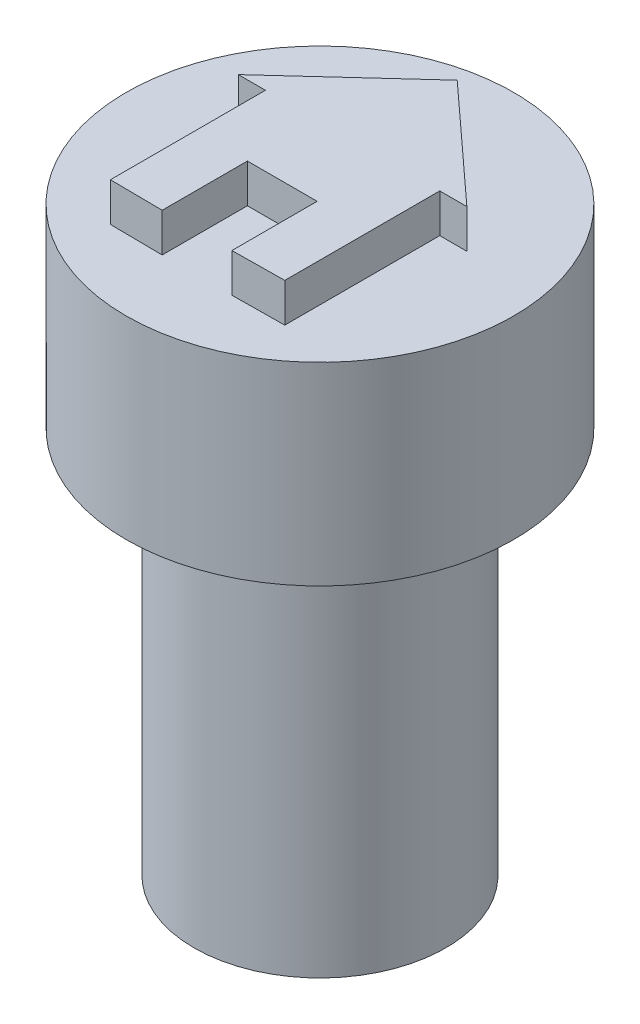
SolidWorks part; units mm, degrees
ref_plane "Front Plane" through (0, 0, 0) normal (0, 0, 1) x (1, 0, 0)
ref_plane "Top Plane" through (0, 0, 0) normal (0, 1, 0) x (1, 0, 0)
ref_plane "Right Plane" through (0, 0, 0) normal (1, 0, 0) x (0, 0, -1)
sketch "Sketch1" plane through (0, 0, 0) normal (0, 1, 0) x (1, 0, 0)
  circle A0 centre (0, 0) radius 3.25
  dimension "D1" = 6.5
extrude "Boss-Extrude1" add sketch "Sketch1" along normal blind 10 contours A0
sketch "Sketch2" plane through (0, 0, 0) normal (0, -1, 0) x (1, 0, 0)
  circle A1 centre (0, 0) radius 1.75
  dimension "D1" = 3.5
extrude "Cut-Extrude1" cut sketch "Sketch2" against normal blind 2.5
sketch "Sketch6" plane through (0, 10, 0) normal (0, 1, 0) x (1, 0, 0)
  circle A0 centre (0, 0) radius 5
  dimension "D1" = 10
extrude "Boss-Extrude2" add sketch "Sketch6" along normal blind 5 contours A0
sketch "Sketch7" plane through (0, 15, 0) normal (0, 1, 0) x (1, 0, 0)
  line L0 (-2.25, 0) -> (2.25, 0) construction
  line L1 (-2.25, 2.25) -> (2.25, 2.25)
  line L2 (-2.25, 2.25) -> (-2.25, -2.25)
  line L3 (-2.25, -2.25) -> (2.25, -2.25)
  line L4 (2.25, 2.25) -> (2.25, -2.25)
  line L5 (-2.25, 2.25) -> (2.25, -2.25) construction
  line L6 (-2.25, -2.25) -> (2.25, 2.25) construction
  line L7 (-2.25, 2.25) -> (-2.25, -2.25)
  point P0 (0, -0.8558)
  dimension "D1" = 4.5
  dimension "D2" = 4.5
sketch "Sketch9" plane through (0, 15, 0) normal (0, 1, 0) x (1, 0, 0)
  line L0 (0, 0.8425) -> (0, 3.5425) construction
  line L1 (-2.25, 0.8425) -> (2.25, 0.8425)
  line L2 (-2.25, 0.8425) -> (-2.25, -3.1575)
  line L3 (-2.25, -3.1575) -> (2.25, -3.1575)
  line L4 (2.25, 0.8425) -> (2.25, -3.1575)
  line L5 (-2.25, 0.8425) -> (2.25, -3.1575) construction
  line L6 (-2.25, -3.1575) -> (2.25, 0.8425) construction
  line L7 (-2.95, 0.8425) -> (0, 3.5425)
  line L8 (2.25, 0.8425) -> (2.95, 0.8425)
  line L9 (-2.25, 0.8425) -> (-2.95, 0.8425)
  line L10 (0, 3.5425) -> (2.95, 0.8425)
  line L12 (-0.9, -3.1724) -> (0.9, -3.1724)
  line L13 (-0.9, -3.1724) -> (-0.9, -0.9724)
  line L14 (-0.9, -0.9724) -> (0.9, -0.9724)
  line L15 (0.9, -3.1724) -> (0.9, -0.9724)
  line L16 (-0.9, -3.1724) -> (0.9, -0.9724) construction
  line L17 (-0.9, -0.9724) -> (0.9, -3.1724) construction
  point P0 (0, -1.1575)
  point P9 (0, -2.0724)
  dimension "D1" = 4
  dimension "D2" = 4.5
  dimension "D3" = 2.7
  dimension "D4" = 0.7
  dimension "D5" = 0.7
  dimension "D6" = 2.2
  dimension "D7" = 1.8
sketch "Sketch12" plane through (0, 15, 0) normal (0, 1, 0) x (1, 0, 0)
  line L0 (0, 3.5425) -> (-2.95, 0.8425)
  line L1 (-2.95, 0.8425) -> (-2.25, 0.8425)
  line L2 (-2.25, 0.8425) -> (-2.25, -3.1575)
  line L3 (-2.25, -3.1575) -> (-0.9, -3.1724)
  line L4 (-0.9, -3.1724) -> (-0.9, -0.9724)
  line L5 (-0.9, -0.9724) -> (0.9, -0.9724)
  line L6 (0.9, -0.9724) -> (0.9, -3.1724)
  line L7 (0.9, -3.1724) -> (2.25, -3.1575)
  line L8 (2.25, -3.1575) -> (2.25, 0.8425)
  line L9 (2.25, 0.8425) -> (2.95, 0.8425)
  line L10 (2.95, 0.8425) -> (0, 3.5425)
extrude "Boss-Extrude3" add sketch "Sketch12" along normal blind 1
